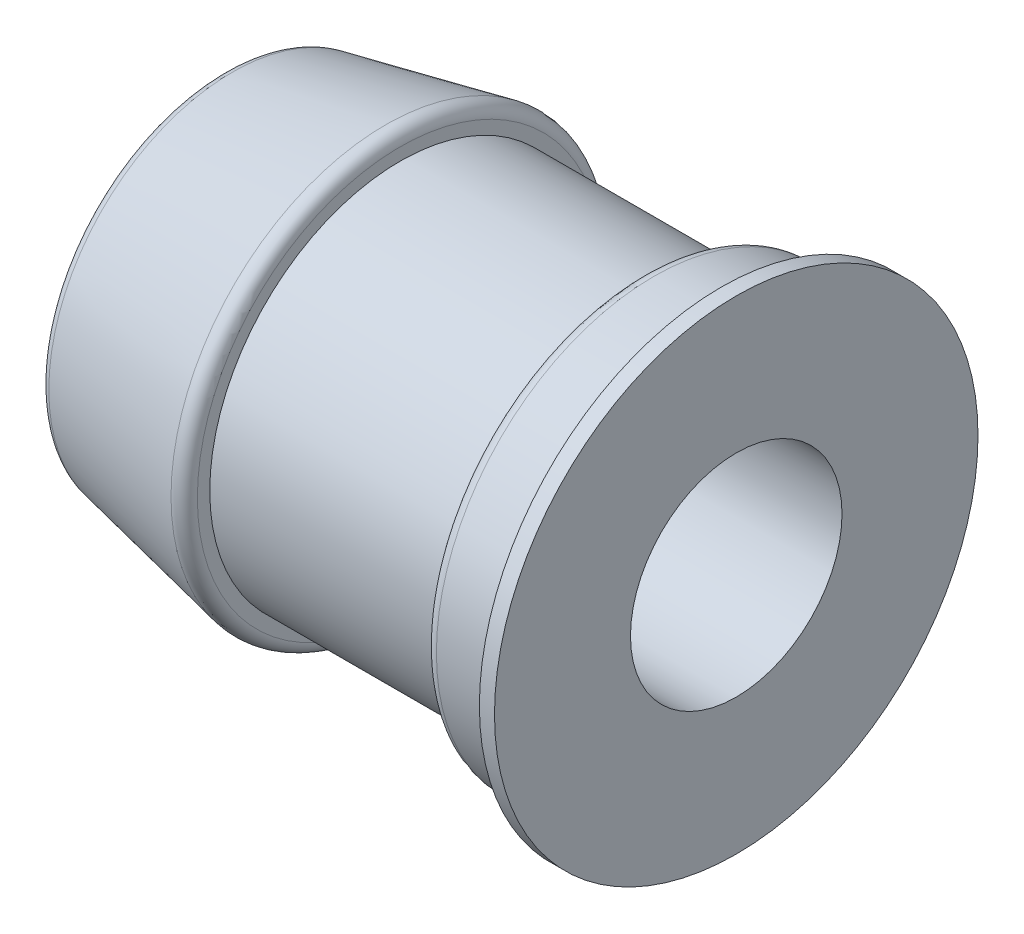
SolidWorks part; units mm, degrees
material "6061 Alloy"
ref_plane "Front Plane" through (0, 0, 0) normal (0, 0, 1) x (1, 0, 0)
ref_plane "Top Plane" through (0, 0, 0) normal (0, 1, 0) x (1, 0, 0)
ref_plane "Right Plane" through (0, 0, 0) normal (1, 0, 0) x (0, 0, -1)
sketch "Sketch1" plane through (0, 0, 0) normal (0, 0, 1) x (1, 0, 0)
  line L0 (-42.201, 0) -> (37.9041, 0) construction
  line L1 (0, -28.9101) -> (0, 27.38) construction
  line L2 (0, 11.1125) -> (22.6124, 11.1125)
  line L3 (-31.3702, 19.05) -> (-31.3702, 15.875)
  line L4 (-31.3702, 19.05) -> (-12.7, 22.86)
  line L5 (-12.7, 22.86) -> (-12.7, 20)
  line L6 (-12.7, 20) -> (12.7, 20)
  line L7 (12.7, 20) -> (12.7, 22.86)
  line L8 (12.7, 22.86) -> (19.5584, 22.86)
  line L9 (19.5584, 22.86) -> (21.0249, 25.4)
  line L10 (21.0249, 25.4) -> (22.6124, 25.4)
  line L11 (22.6124, 25.4) -> (22.6124, 11.1125)
  line L12 (-31.3702, 15.875) -> (0, 15.875)
  line L13 (0, 15.875) -> (0, 11.1125)
  dimension "D1" = 15.875
  dimension "D2" = 11.1125
  dimension "D3" = 20
  dimension "D4" = 25.4
  dimension "D5" = 53.9826
  dimension "D6" = 22.86
  dimension "D7" = 19.05
  dimension "D8" = 31.3702
  dimension "D9" = 12.7
  dimension "D10" = 25.4
  dimension "D11" = 60
  dimension "D12" = 1.5875
revolve "Revolve1" add sketch "Sketch1" angle 360 about L0
fillet "Fillet1" radius 1.27 3 edges at (12.7, 0, 22.86) (-12.7, 0, 22.86) (-31.3702, 0, 19.05)
